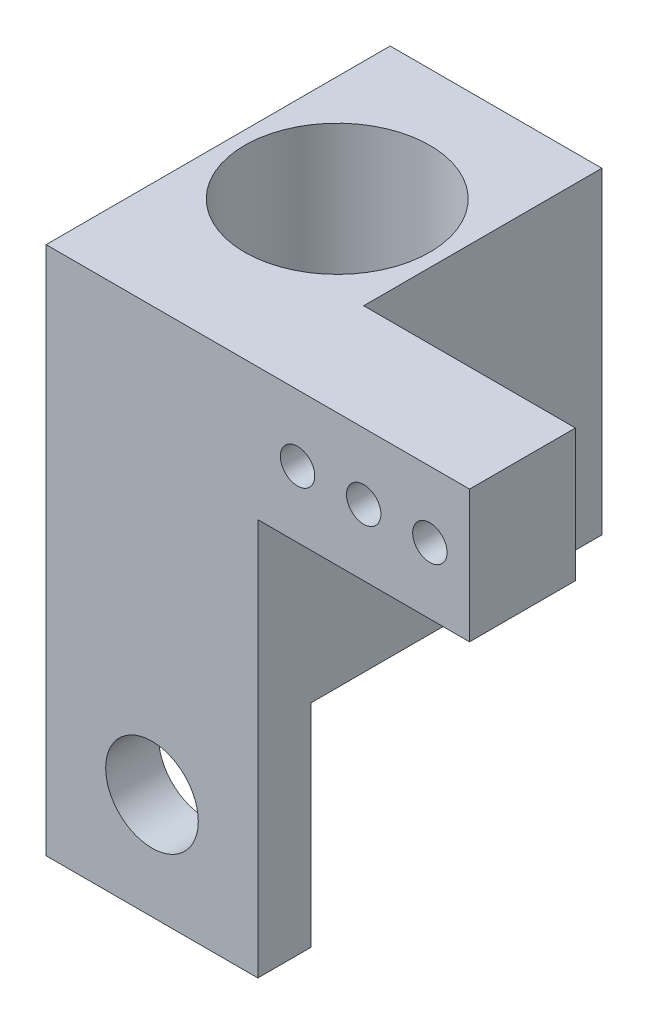
SolidWorks part; units mm, degrees
ref_plane "Front Plane" through (0, 0, 0) normal (0, 0, 1) x (1, 0, 0)
ref_plane "Top Plane" through (0, 0, 0) normal (0, 1, 0) x (1, 0, 0)
ref_plane "Right Plane" through (0, 0, 0) normal (1, 0, 0) x (0, 0, -1)
sketch "Sketch1" plane through (0, 0, 0) normal (0, 1, 0) x (1, 0, 0)
  line L0 (-16, 0) -> (0, 0)
  line L1 (-16, 8) -> (-8, 8)
  line L2 (-16, 8) -> (-16, 0)
  line L4 (-8, 8) -> (-8, 1)
  line L6 (0, 0) -> (0, 1)
  line L7 (0, 1) -> (-8, 1)
  dimension "D1" = 8
  dimension "D2" = 8
  dimension "D3" = 1
  dimension "D4" = 8
  dimension "D5" = 0
  dimension "D6" = 0
extrude "Boss-Extrude1" add sketch "Sketch1" along normal blind 2
sketch "Sketch2" plane through (0, 2, 0) normal (0, 1, 0) x (1, 0, 0)
  line L0 (-16, 0) -> (0, 0) construction
  line L1 (-16, 8) -> (-8, 8)
  line L2 (-16, 8) -> (-16, 0)
  line L3 (-16, 0) -> (-8, 0)
  line L4 (-8, 8) -> (-8, 0)
extrude "Boss-Extrude2" add sketch "Sketch2" along normal blind 2
sketch "Sketch3" plane through (0, 0, 0) normal (0, -1, 0) x (1, 0, 0)
  line L1 (-8, -8) -> (-16, -8)
  line L2 (-8, -8) -> (-8, 0)
  line L3 (-8, 0) -> (-16, 0)
  line L4 (-16, -8) -> (-16, 0)
extrude "Boss-Extrude3" add sketch "Sketch3" along normal blind 8
sketch "Sketch4" plane through (0, 4, 0) normal (0, 1, 0) x (1, 0, 0)
  line L0 (-8, 8) -> (-16, 8) construction
  line L1 (-8, 0) -> (-8, 8) construction
  circle A0 centre (-12, 4) radius 3.5
  dimension "D1" = 4
  dimension "D2" = 4
  dimension "D3" = 7
extrude "Cut-Extrude1" cut sketch "Sketch4" against normal blind 10
sketch "Sketch5" plane through (0, -6, 0) normal (0, 1, 0) x (1, 0, 0)
  line L0 (-8, 8) -> (-16, 8) construction
  line L1 (-16, 8) -> (-16, 0) construction
  circle A0 centre (-13.5, 4) radius 0.65
  circle A1 centre (-10.5, 4) radius 0.65
  dimension "D1" = 1.3
  dimension "D2" = 1.3
  dimension "D4" = 4
  dimension "D5" = 2.5
  dimension "D3" = 3
extrude "Cut-Extrude2" cut sketch "Sketch5" against normal up to next
sketch "Sketch6" plane through (0, 0, -1) normal (0, 0, -1) x (-1, 0, 0)
  line L0 (0, 0) -> (8, 0) construction
  line L1 (0, 2) -> (0, 0) construction
  circle A0 centre (6.5, 1) radius 0.65
  circle A1 centre (4, 1) radius 0.65
  circle A2 centre (1.5, 1) radius 0.65
  dimension "D1" = 1.3
  dimension "D2" = 1
  dimension "D3" = 6.5
  dimension "D4" = 2.5
  dimension "D5" = 1.5
  dimension "D6" = 1.3
  dimension "D7" = 1.3
extrude "Cut-Extrude3" cut sketch "Sketch6" against normal up to next
sketch "Sketch10" plane through (0, 0, 0) normal (0, 0, 1) x (1, 0, 0)
  line L0 (-8, 2) -> (-16, 2)
  line L1 (-16, 4) -> (-16, -8) construction
  line L2 (-16, 2) -> (-16, -8)
  line L3 (-16, -8) -> (-8, -8)
  line L4 (-8, -8) -> (-8, 0) construction
  line L5 (-8, -8) -> (-16, -8) construction
  line L6 (-8, -8) -> (-8, 0)
  line L7 (-8, 0) -> (0, 0)
  line L8 (0, 0) -> (0, 2)
  line L9 (0, 2) -> (-8, 2)
  circle A0 centre (-1.5, 1) radius 0.65
  circle A1 centre (-4, 1) radius 0.65
  circle A2 centre (-6.5, 1) radius 0.65
  dimension "D1" = 1.3
  dimension "D2" = 1.3
  dimension "D3" = 1.3
extrude "Boss-Extrude6" add sketch "Sketch10" along normal blind 3
sketch "Sketch11" plane through (0, -8, 0) normal (0, -1, 0) x (1, 0, 0)
  line L0 (-16, 3) -> (-16, -8) construction
  line L1 (-8, 3) -> (-16, 3)
  line L2 (-8, 3) -> (-8, 1)
  line L3 (-8, 1) -> (-16, 1)
  line L4 (-16, 3) -> (-16, 1)
  dimension "D1" = 2
extrude "Boss-Extrude7" add sketch "Sketch11" along normal blind 8
sketch "Sketch12" plane through (0, 0, 1) normal (0, 0, -1) x (-1, 0, 0)
  line L0 (8, -16) -> (8, -8) construction
  line L1 (16, -16) -> (8, -16) construction
  circle A0 centre (12, -12) radius 1
  dimension "D1" = 4
  dimension "D2" = 2
  dimension "D3" = 4
extrude "Cut-Extrude5" cut sketch "Sketch12" against normal blind 8
sketch "Sketch13" plane through (0, 0, -8) normal (0, 0, -1) x (-1, 0, 0)
  line L1 (8, -8) -> (16, -8)
  line L2 (8, -8) -> (8, 4)
  line L3 (8, 4) -> (16, 4)
  line L4 (16, -8) -> (16, 4)
extrude "Boss-Extrude8" add sketch "Sketch13" along normal blind 2
sketch "Sketch14" plane through (0, 0, 0) normal (0, -1, 0) x (1, 0, 0)
  line L1 (0, -1) -> (-8, -1)
  line L2 (0, -1) -> (0, 3)
  line L3 (0, 3) -> (-8, 3)
  line L4 (-8, -1) -> (-8, 3)
extrude "Boss-Extrude9" add sketch "Sketch14" along normal blind 1
sketch "Sketch15" plane through (0, 2, 0) normal (0, 1, 0) x (1, 0, 0)
  line L0 (-8, 0) -> (-8, 1)
  line L1 (-8, 0) -> (-8, 1) construction
  line L2 (-8, 1) -> (0, 1)
  line L3 (0, 1) -> (0, -3)
  line L4 (0, -3) -> (-16, -3)
  line L5 (-16, -3) -> (-16, 0)
  line L6 (-16, 0) -> (-8, 0)
extrude "Boss-Extrude10" add sketch "Sketch15" along normal up to surface (2 mm away) up to face at (-12, 4, -0.5)
sketch "Sketch18" plane through (0, 0, -1) normal (0, 0, -1) x (-1, 0, 0)
  circle A0 centre (1.5, 1) radius 0.65
  circle A1 centre (4, 1) radius 0.65
  circle A2 centre (6.5, 1) radius 0.65
  dimension "D1" = 1.3
  dimension "D2" = 1.3
  dimension "D3" = 1.3
extrude "Boss-Extrude11" add sketch "Sketch18" against normal up to surface (4 mm away) up to face at (-11, -12, 3)
sketch "Sketch19" plane through (0, 0, -1) normal (0, 0, -1) x (-1, 0, 0)
  line L0 (0, 4) -> (0, -1) construction
  line L1 (8, -1) -> (0, -1) construction
  circle A0 centre (1.5, 1.5) radius 0.65
  circle A1 centre (4, 1.5) radius 0.65
  circle A2 centre (6.5, 1.5) radius 0.65
  dimension "D1" = 1.3
  dimension "D2" = 1.3
  dimension "D3" = 1.3
  dimension "D4" = 2.5
  dimension "D5" = 2.5
  dimension "D7" = 2.5
  dimension "D6" = 1.5
extrude "Cut-Extrude6" cut sketch "Sketch19" against normal up to next
sketch "Sketch20" plane through (0, 0, 1) normal (0, 0, -1) x (-1, 0, 0)
  circle A0 centre (12, -12) radius 1.75
  dimension "D1" = 3.5
extrude "Cut-Extrude7" cut sketch "Sketch20" against normal up to next
sketch "Sketch21" plane through (0, 4, 0) normal (0, 1, 0) x (1, 0, 0)
  circle A0 centre (-12, 4) radius 3.5
  dimension "D1" = 7
